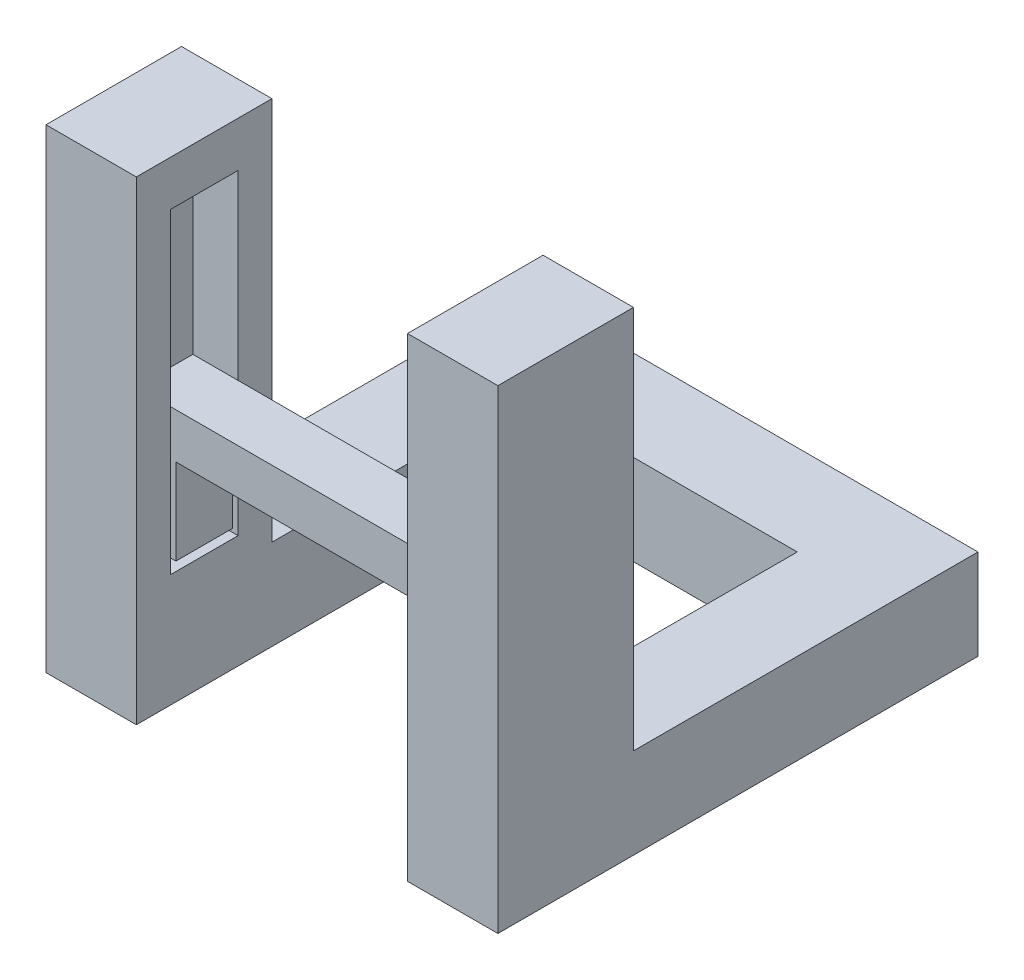
SolidWorks part; units mm, degrees
ref_plane "Front Plane" through (0, 0, 0) normal (0, 0, 1) x (1, 0, 0)
ref_plane "Top Plane" through (0, 0, 0) normal (0, 1, 0) x (1, 0, 0)
ref_plane "Right Plane" through (0, 0, 0) normal (1, 0, 0) x (0, 0, -1)
sketch "Sketch1" plane through (0, 0, 0) normal (0, 1, 0) x (1, 0, 0)
  line L1 (0, 0) -> (20, 0)
  line L2 (0, 0) -> (0, 6)
  line L3 (0, 6) -> (20, 6)
  line L4 (20, 0) -> (20, 6)
  line L5 (4, 6) -> (16, 6)
  line L6 (4, 6) -> (4, 0)
  line L7 (4, 0) -> (16, 0)
  line L8 (16, 6) -> (16, 0)
  dimension "D1" = 4
  dimension "20" = 20
  dimension "D2" = 6
  dimension "D3" = 4
  dimension "D4" = 12
extrude "Boss-Extrude1" add sketch "Sketch1" along normal blind 13 contours L3 L8 L1 L4 | L6 L3 L2 L1
sketch "Sketch2" plane through (0, 13, 0) normal (0, 1, 0) x (1, 0, 0)
  line L0 (16, 6) -> (16, 0) construction
  line L1 (16, 1.5) -> (18, 1.5)
  line L2 (16, 1.5) -> (16, 4.5)
  line L3 (16, 4.5) -> (18, 4.5)
  line L4 (18, 1.5) -> (18, 4.5)
  line L5 (20, 0) -> (0, 0) construction
  line L6 (10, 0) -> (10, 6.0872) construction
  line L7 (16, 6) -> (20, 6) construction
  line L8 (20, 0) -> (20, 6) construction
  line L9 (16, 1.5) -> (16, 4.5)
  line L10 (2, 1.5) -> (2, 4.5)
  line L11 (4, 4.5) -> (2, 4.5)
  line L12 (4, 1.5) -> (4, 4.5)
  line L13 (4, 1.5) -> (2, 1.5)
  line L14 (4, 1.5) -> (4, 4.5)
  line M6 (4, 0) -> (4, 6)
  dimension "D1" = 1.5
  dimension "D2" = 1.5
  dimension "D3" = 2
extrude "Cut-Extrude1" cut sketch "Sketch2" against normal blind 4 contours L1 L4 L3 L2 | L13 L11 L10 M6
sketch "Sketch4" plane through (0, 9, 0) normal (0, 1, 0) x (1, 0, 0)
  line L0 (16, 1.5) -> (16, 4.5) construction
  line L1 (16, 1.75) -> (17.75, 1.75)
  line L2 (16, 1.75) -> (16, 4.25)
  line L3 (16, 4.25) -> (17.75, 4.25)
  line L4 (17.75, 1.75) -> (17.75, 4.25)
  line L5 (16, 1.5) -> (18, 1.5) construction
  line L6 (18, 1.5) -> (18, 4.5) construction
  line L7 (16, 4.5) -> (18, 4.5) construction
  line L8 (20, 0) -> (0, 0) construction
  line L9 (16, 0) -> (20, 0) construction
  line L10 (0, 0) -> (10, 0) construction
  line L11 (10, 0) -> (10, 6.0812) construction
  line L12 (16, 1.75) -> (16, 4.25)
  line L13 (2.25, 1.75) -> (2.25, 4.25)
  line L14 (4, 4.25) -> (2.25, 4.25)
  line L15 (4, 1.75) -> (4, 4.25)
  line L16 (4, 1.75) -> (2.25, 1.75)
  line L17 (4, 1.75) -> (4, 4.25)
  line M8 (16, 4.5) -> (16, 1.5)
  dimension "D1" = 0.25
  dimension "D2" = 0.25
  dimension "D3" = 0.25
extrude "Boss-Extrude2" add sketch "Sketch4" along direction (0, 1, 0) on the side of the normal blind 4.2 separate body contours L1 L4 L3 M8 | L16 L15 L14 L13
sketch "Sketch5" plane through (0, 13.2, 0) normal (0, 1, 0) x (1, 0, 0)
  line L1 (17.75, 1.75) -> (2.25, 1.75)
  line L2 (17.75, 1.75) -> (17.75, 4.25)
  line L3 (17.75, 4.25) -> (2.25, 4.25)
  line L4 (2.25, 1.75) -> (2.25, 4.25)
extrude "Boss-Extrude3" add sketch "Sketch5" along normal blind 2
sketch "Sketch7" plane through (0, 13, 0) normal (0, 1, 0) x (1, 0, 0)
  line L0 (16, 4.5) -> (16, 6)
  line L1 (20, 0) -> (16, 0)
  line L2 (20, 0) -> (20, 6)
  line L3 (20, 6) -> (16, 6)
  line L4 (16, 0) -> (16, 1.5)
  line L5 (4, 6) -> (0, 6)
  line L6 (4, 6) -> (4, 4.5)
  line L7 (4, 0) -> (0, 0)
  line L8 (0, 6) -> (0, 0)
  line L9 (4, 1.5) -> (2, 1.5)
  line L11 (4, 4.5) -> (2, 4.5)
  line L12 (2, 1.5) -> (2, 4.5)
  line L13 (16, 1.5) -> (18, 1.5)
  line L15 (16, 4.5) -> (18, 4.5)
  line L16 (18, 1.5) -> (18, 4.5)
  line L17 (4, 1.5) -> (4, 0)
extrude "Boss-Extrude4" add sketch "Sketch7" along normal blind 10
sketch "Sketch8" plane through (0, 0, 0) normal (0, -1, 0) x (1, 0, 0)
  line L1 (0, -6) -> (4, -6)
  line L2 (0, -6) -> (0, 0)
  line L3 (0, 0) -> (4, 0)
  line L4 (4, -6) -> (4, 0)
  line L5 (16, -6) -> (20, -6)
  line L6 (16, -6) -> (16, 0)
  line L7 (16, 0) -> (20, 0)
  line L8 (20, -6) -> (20, 0)
extrude "Cut-Extrude2" cut sketch "Sketch8" against normal blind 4
sketch "Sketch9" plane through (4, 0, 0) normal (1, 0, 0) x (0, 0, -1)
  line L0 (4.25, 13.2) -> (4.25, 9) construction
  line L1 (1.75, 9) -> (4.25, 9)
  line L2 (1.75, 9) -> (1.75, 9.4)
  line L3 (1.75, 9.4) -> (4.25, 9.4)
  line L4 (4.25, 9) -> (4.25, 9.4)
  dimension "D1" = 0.4
extrude "Cut-Extrude3" cut sketch "Sketch9" against normal up to next
sketch "Sketch10" plane through (16, 0, 0) normal (-1, 0, 0) x (0, 0, 1)
  line L0 (-1.75, 13.2) -> (-1.75, 9) construction
  line L1 (-4.25, 9) -> (-1.75, 9)
  line L2 (-4.25, 9) -> (-4.25, 9.4)
  line L3 (-4.25, 9.4) -> (-1.75, 9.4)
  line L4 (-1.75, 9) -> (-1.75, 9.4)
  dimension "D1" = 0.4
extrude "Cut-Extrude4" cut sketch "Sketch10" against normal up to next (2 mm away)
sketch "Sketch12" plane through (0, 4, 0) normal (0, -1, 0) x (1, 0, 0)
  line L0 (4, -4.5) -> (4, -6) construction
  line L1 (20, -6) -> (0, -6)
  line L2 (20, -6) -> (20, -21.25)
  line L3 (20, -21.25) -> (0, -21.25)
  line L4 (0, -6) -> (0, -21.25)
  line L5 (16, -6) -> (4, -6)
  line L6 (16, -6) -> (16, -17.25)
  line L7 (16, -17.25) -> (4, -17.25)
  line L8 (4, -6) -> (4, -17.25)
  line L9 (0, -6) -> (0, 0) construction
  line L10 (17.75, -4.25) -> (2.25, -4.25) construction
  line M6 (0, -6) -> (4, -6)
  dimension "D1" = 4
  dimension "D2" = 13
extrude "Boss-Extrude5" add sketch "Sketch12" against normal blind 4 contours L8 L4 L3 L2 L1 L6 L7 M6
sketch "Sketch14" plane through (0, 23, 0) normal (0, 1, 0) x (1, 0, 0)
  line L0 (16, 0) -> (20, 0) construction
  line L1 (20, 6) -> (16, 6)
  line L2 (20, 6) -> (20, 0)
  line L3 (20, 0) -> (16, 0)
  line L4 (16, 6) -> (16, 0)
  line L6 (4, 6) -> (0, 6)
  line L7 (4, 6) -> (4, 0)
  line L8 (4, 0) -> (0, 0)
  line L9 (0, 6) -> (0, 0)
extrude "Boss-Extrude7" add sketch "Sketch14" along normal blind 2
